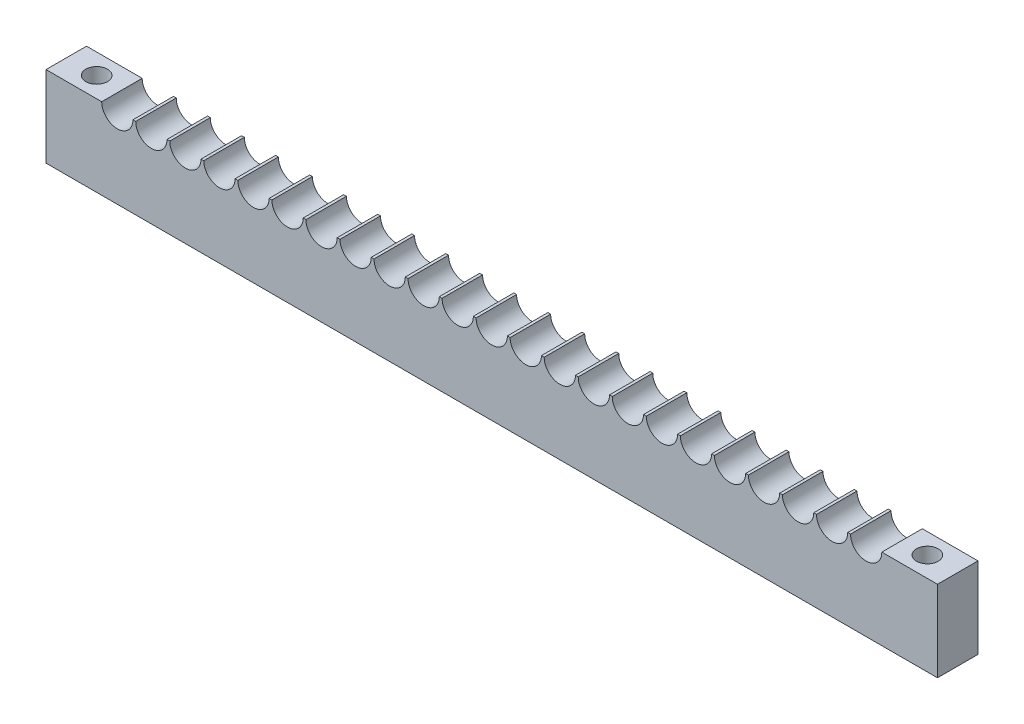
SolidWorks part; units mm, degrees
ref_plane "Front Plane" through (0, 0, 0) normal (0, 0, 1) x (1, 0, 0)
ref_plane "Top Plane" through (0, 0, 0) normal (0, 1, 0) x (1, 0, 0)
ref_plane "Right Plane" through (0, 0, 0) normal (1, 0, 0) x (0, 0, -1)
sketch "Sketch1" plane through (0, 0, 0) normal (0, 0, 1) x (1, 0, 0)
  line L1 (69.85, -6.35) -> (-69.85, -6.35)
  line L2 (69.85, -6.35) -> (69.85, 6.35)
  line L3 (69.85, 6.35) -> (-69.85, 6.35)
  line L4 (-69.85, -6.35) -> (-69.85, 6.35)
  line L5 (69.85, -6.35) -> (-69.85, 6.35) construction
  line L6 (69.85, 6.35) -> (-69.85, -6.35) construction
  point P0 (0, 0)
  dimension "D1" = 139.7
  dimension "D2" = 12.7
extrude "Boss-Extrude1" add sketch "Sketch1" along normal blind 6.35
sketch "Sketch2" plane through (0, 0, 6.35) normal (0, 0, 1) x (1, 0, 0)
  line L0 (-69.85, 6.35) -> (69.85, 6.35) construction
  line L1 (-69.85, 6.35) -> (-69.85, -6.35) construction
  line L2 (69.85, -6.35) -> (69.85, 6.35) construction
  line L3 (0, 6.35) -> (0, -6.35) construction
  line L4 (69.85, 6.35) -> (-69.85, 6.35) construction
  line L5 (-69.85, -6.35) -> (69.85, -6.35) construction
  circle A0 centre (0, 6.35) radius 2.4511
  circle A1 centre (5.334, 6.35) radius 2.4511
  circle A2 centre (10.668, 6.35) radius 2.4511
  circle A3 centre (16.002, 6.35) radius 2.4511
  circle A4 centre (21.336, 6.35) radius 2.4511
  circle A5 centre (26.67, 6.35) radius 2.4511
  circle A6 centre (32.004, 6.35) radius 2.4511
  circle A7 centre (37.338, 6.35) radius 2.4511
  circle A8 centre (42.672, 6.35) radius 2.4511
  circle A9 centre (48.006, 6.35) radius 2.4511
  circle A10 centre (53.34, 6.35) radius 2.4511
  circle A11 centre (58.674, 6.35) radius 2.4511
  circle A13 centre (0, 6.35) radius 2.4511
  circle A14 centre (5.334, 6.35) radius 2.4511
  circle A15 centre (10.668, 6.35) radius 2.4511
  circle A16 centre (16.002, 6.35) radius 2.4511
  circle A17 centre (21.336, 6.35) radius 2.4511
  circle A18 centre (26.67, 6.35) radius 2.4511
  circle A19 centre (32.004, 6.35) radius 2.4511
  circle A20 centre (37.338, 6.35) radius 2.4511
  circle A21 centre (42.672, 6.35) radius 2.4511
  circle A22 centre (48.006, 6.35) radius 2.4511
  circle A23 centre (53.34, 6.35) radius 2.4511
  circle A25 centre (-5.334, 6.35) radius 2.4511
  circle A26 centre (0, 6.35) radius 2.4511
  circle A27 centre (5.334, 6.35) radius 2.4511
  circle A28 centre (10.668, 6.35) radius 2.4511
  circle A29 centre (16.002, 6.35) radius 2.4511
  circle A30 centre (21.336, 6.35) radius 2.4511
  circle A31 centre (26.67, 6.35) radius 2.4511
  circle A32 centre (32.004, 6.35) radius 2.4511
  circle A33 centre (37.338, 6.35) radius 2.4511
  circle A34 centre (42.672, 6.35) radius 2.4511
  circle A35 centre (48.006, 6.35) radius 2.4511
  circle A37 centre (-10.668, 6.35) radius 2.4511
  circle A38 centre (-5.334, 6.35) radius 2.4511
  circle A39 centre (0, 6.35) radius 2.4511
  circle A40 centre (5.334, 6.35) radius 2.4511
  circle A41 centre (10.668, 6.35) radius 2.4511
  circle A42 centre (16.002, 6.35) radius 2.4511
  circle A43 centre (21.336, 6.35) radius 2.4511
  circle A44 centre (26.67, 6.35) radius 2.4511
  circle A45 centre (32.004, 6.35) radius 2.4511
  circle A46 centre (37.338, 6.35) radius 2.4511
  circle A47 centre (42.672, 6.35) radius 2.4511
  circle A49 centre (-16.002, 6.35) radius 2.4511
  circle A50 centre (-10.668, 6.35) radius 2.4511
  circle A51 centre (-5.334, 6.35) radius 2.4511
  circle A52 centre (0, 6.35) radius 2.4511
  circle A53 centre (5.334, 6.35) radius 2.4511
  circle A54 centre (10.668, 6.35) radius 2.4511
  circle A55 centre (16.002, 6.35) radius 2.4511
  circle A56 centre (21.336, 6.35) radius 2.4511
  circle A57 centre (26.67, 6.35) radius 2.4511
  circle A58 centre (32.004, 6.35) radius 2.4511
  circle A59 centre (37.338, 6.35) radius 2.4511
  circle A61 centre (-21.336, 6.35) radius 2.4511
  circle A62 centre (-16.002, 6.35) radius 2.4511
  circle A63 centre (-10.668, 6.35) radius 2.4511
  circle A64 centre (-5.334, 6.35) radius 2.4511
  circle A65 centre (0, 6.35) radius 2.4511
  circle A66 centre (5.334, 6.35) radius 2.4511
  circle A67 centre (10.668, 6.35) radius 2.4511
  circle A68 centre (16.002, 6.35) radius 2.4511
  circle A69 centre (21.336, 6.35) radius 2.4511
  circle A70 centre (26.67, 6.35) radius 2.4511
  circle A71 centre (32.004, 6.35) radius 2.4511
  circle A73 centre (-26.67, 6.35) radius 2.4511
  circle A74 centre (-21.336, 6.35) radius 2.4511
  circle A75 centre (-16.002, 6.35) radius 2.4511
  circle A76 centre (-10.668, 6.35) radius 2.4511
  circle A77 centre (-5.334, 6.35) radius 2.4511
  circle A78 centre (0, 6.35) radius 2.4511
  circle A79 centre (5.334, 6.35) radius 2.4511
  circle A80 centre (10.668, 6.35) radius 2.4511
  circle A81 centre (16.002, 6.35) radius 2.4511
  circle A82 centre (21.336, 6.35) radius 2.4511
  circle A83 centre (26.67, 6.35) radius 2.4511
  circle A85 centre (-32.004, 6.35) radius 2.4511
  circle A86 centre (-26.67, 6.35) radius 2.4511
  circle A87 centre (-21.336, 6.35) radius 2.4511
  circle A88 centre (-16.002, 6.35) radius 2.4511
  circle A89 centre (-10.668, 6.35) radius 2.4511
  circle A90 centre (-5.334, 6.35) radius 2.4511
  circle A91 centre (0, 6.35) radius 2.4511
  circle A92 centre (5.334, 6.35) radius 2.4511
  circle A93 centre (10.668, 6.35) radius 2.4511
  circle A94 centre (16.002, 6.35) radius 2.4511
  circle A95 centre (21.336, 6.35) radius 2.4511
  circle A97 centre (-37.338, 6.35) radius 2.4511
  circle A98 centre (-32.004, 6.35) radius 2.4511
  circle A99 centre (-26.67, 6.35) radius 2.4511
  circle A100 centre (-21.336, 6.35) radius 2.4511
  circle A101 centre (-16.002, 6.35) radius 2.4511
  circle A102 centre (-10.668, 6.35) radius 2.4511
  circle A103 centre (-5.334, 6.35) radius 2.4511
  circle A104 centre (0, 6.35) radius 2.4511
  circle A105 centre (5.334, 6.35) radius 2.4511
  circle A106 centre (10.668, 6.35) radius 2.4511
  circle A107 centre (16.002, 6.35) radius 2.4511
  circle A109 centre (-42.672, 6.35) radius 2.4511
  circle A110 centre (-37.338, 6.35) radius 2.4511
  circle A111 centre (-32.004, 6.35) radius 2.4511
  circle A112 centre (-26.67, 6.35) radius 2.4511
  circle A113 centre (-21.336, 6.35) radius 2.4511
  circle A114 centre (-16.002, 6.35) radius 2.4511
  circle A115 centre (-10.668, 6.35) radius 2.4511
  circle A116 centre (-5.334, 6.35) radius 2.4511
  circle A117 centre (0, 6.35) radius 2.4511
  circle A118 centre (5.334, 6.35) radius 2.4511
  circle A119 centre (10.668, 6.35) radius 2.4511
  circle A121 centre (-48.006, 6.35) radius 2.4511
  circle A122 centre (-42.672, 6.35) radius 2.4511
  circle A123 centre (-37.338, 6.35) radius 2.4511
  circle A124 centre (-32.004, 6.35) radius 2.4511
  circle A125 centre (-26.67, 6.35) radius 2.4511
  circle A126 centre (-21.336, 6.35) radius 2.4511
  circle A127 centre (-16.002, 6.35) radius 2.4511
  circle A128 centre (-10.668, 6.35) radius 2.4511
  circle A129 centre (-5.334, 6.35) radius 2.4511
  circle A130 centre (0, 6.35) radius 2.4511
  circle A131 centre (5.334, 6.35) radius 2.4511
  circle A133 centre (-53.34, 6.35) radius 2.4511
  circle A134 centre (-48.006, 6.35) radius 2.4511
  circle A135 centre (-42.672, 6.35) radius 2.4511
  circle A136 centre (-37.338, 6.35) radius 2.4511
  circle A137 centre (-32.004, 6.35) radius 2.4511
  circle A138 centre (-26.67, 6.35) radius 2.4511
  circle A139 centre (-21.336, 6.35) radius 2.4511
  circle A140 centre (-16.002, 6.35) radius 2.4511
  circle A141 centre (-10.668, 6.35) radius 2.4511
  circle A142 centre (-5.334, 6.35) radius 2.4511
  circle A143 centre (0, 6.35) radius 2.4511
  circle A157 centre (-5.334, 6.35) radius 2.4511
  circle A158 centre (-10.668, 6.35) radius 2.4511
  circle A159 centre (-16.002, 6.35) radius 2.4511
  circle A160 centre (-21.336, 6.35) radius 2.4511
  circle A161 centre (-26.67, 6.35) radius 2.4511
  circle A162 centre (-32.004, 6.35) radius 2.4511
  circle A163 centre (-37.338, 6.35) radius 2.4511
  circle A164 centre (-42.672, 6.35) radius 2.4511
  circle A165 centre (-48.006, 6.35) radius 2.4511
  circle A166 centre (-53.34, 6.35) radius 2.4511
  circle A167 centre (-58.674, 6.35) radius 2.4511
  dimension "D1" = 4.9022
  dimension "D2" = 12
  dimension "D3" = 12
extrude "Cut-Extrude1" cut sketch "Sketch2" against normal through all
hole_wizard "M3 Clearance Hole1" positions "Sketch3" profile "Sketch4" hole size "M3" standard "ANSI Metric" end condition through all
sketch "Sketch3" plane through (0, -6.35, 0) normal (0, -1, 0) x (-1, 0, 0)
  line L0 (69.85, -3.175) -> (-69.85, -3.175) construction
  line L1 (69.85, -6.35) -> (69.85, 0) construction
  line L2 (-69.85, -6.35) -> (-69.85, 0) construction
  point P9 (65.0875, -3.175)
  dimension "D1" = 4.7625
sketch "Sketch4" plane through (-65.0875, -6.35, 3.175) normal (1, 0, 0) x (0, 0, -1)
  line L0 (0, 0) -> (0, 12.7)
  line L1 (0, 12.7) -> (1.7, 12.7)
  line L2 (1.7, 12.7) -> (1.7, 0)
  line L5 (1.7, 0) -> (0, 0)
  line L11 (0, -6.35) -> (0, 107.95) construction
  dimension "Thru Hole Dia." = 3.4
  dimension "Thru Hole Depth" = 12.7
mirror "Mirror1" about plane through (0, 0, 0) normal (1, 0, 0) of "M3 Clearance Hole1"
